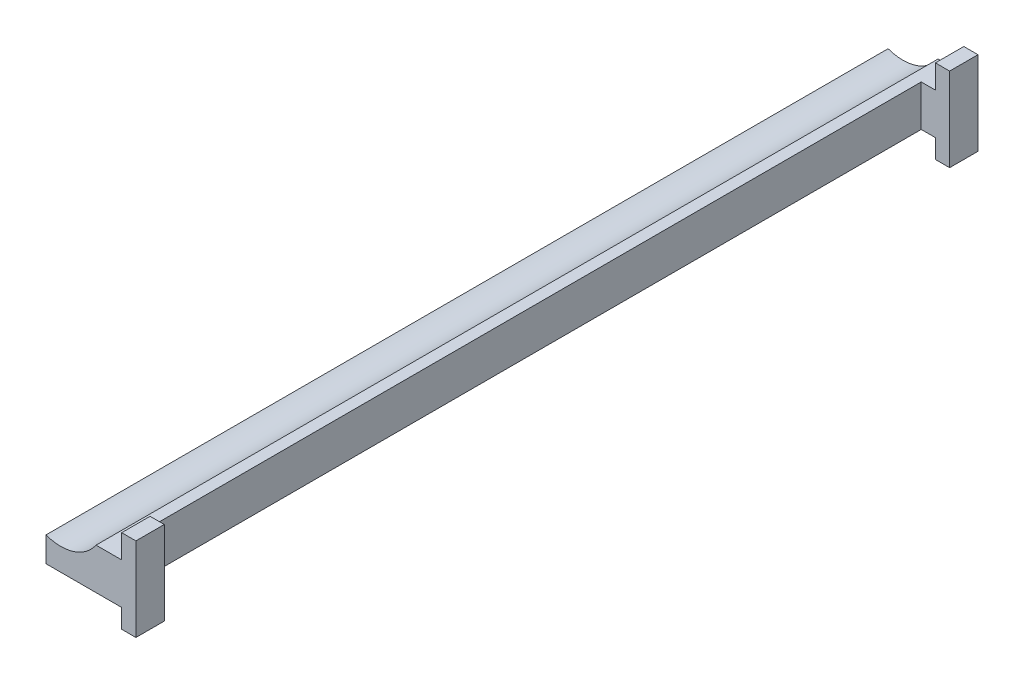
SolidWorks part; units mm, degrees
ref_plane "Front Plane" through (0, 0, 0) normal (0, 0, 1) x (1, 0, 0)
ref_plane "Top Plane" through (0, 0, 0) normal (0, 1, 0) x (1, 0, 0)
ref_plane "Right Plane" through (0, 0, 0) normal (1, 0, 0) x (0, 0, -1)
sketch "Sketch1" plane through (0, 0, 0) normal (0, 0, 1) x (1, 0, 0)
  line L0 (0, 0) -> (187.42, 0) construction
  line L1 (0, 138.5306) -> (0, -235.9813) construction
  line L2 (187.42, 0) -> (263.25, 0) construction
  line L3 (0, 0) -> (-187.4152, -1.3411) construction
  line L4 (-266.206, -1.905) -> (-266.85, -1.9096) construction
  line L5 (-187.4152, 42.88) -> (-187.4152, -45.5623)
  line L6 (-266.85, -1.9096) -> (-266.85, 43.0904) construction
  line L7 (-187.4152, -45.5623) -> (-202.4152, -45.5623)
  line L8 (-202.4152, -45.5623) -> (-202.4152, -25.5623)
  line L9 (-202.4152, -25.5623) -> (-282.4152, -25.5623)
  line L10 (-282.4152, -25.5623) -> (-282.4152, 0.8681)
  line L12 (-202.4152, 17.9396) -> (-202.4152, 42.88)
  line L13 (-202.4152, 42.88) -> (-187.4152, 42.88)
  line L14 (-229.5346, 17.9396) -> (-202.4152, 17.9396)
  arc A1 (-282.4152, 0.8681) -> (-229.5346, 17.9396) centre (-266.85, 43.0904) ccw
  arc A2 (0, -225.3) -> (225.3, 0) centre (0, 0) ccw
  dimension "D1" = 187.42
  dimension "D4" = 44.22
  dimension "D3" = 263.25
  dimension "D5" = 266.85
  dimension "D6" = 44.22
extrude "Boss-Extrude1" add sketch "Sketch1" against normal blind 890 contours A1 L10 L9 L8 L7 L5 L13 L12 L14
sketch "Sketch4" plane through (-187.4152, 0, 0) normal (1, 0, 0) x (0, 0, -1)
  line L1 (890, 42.88) -> (0, 42.88) construction
  line L2 (30, 42.88) -> (30, -45.5623)
  line L3 (890, -45.5623) -> (0, -45.5623) construction
  line L4 (30, -45.5623) -> (860, -45.5623)
  line L5 (860, -45.5623) -> (860, 42.88)
  line L6 (860, 42.88) -> (30, 42.88)
  line L7 (890, 42.88) -> (890, -45.5623) construction
  dimension "D1" = 30
extrude "Cut-Extrude1" cut sketch "Sketch4" against normal blind 30
